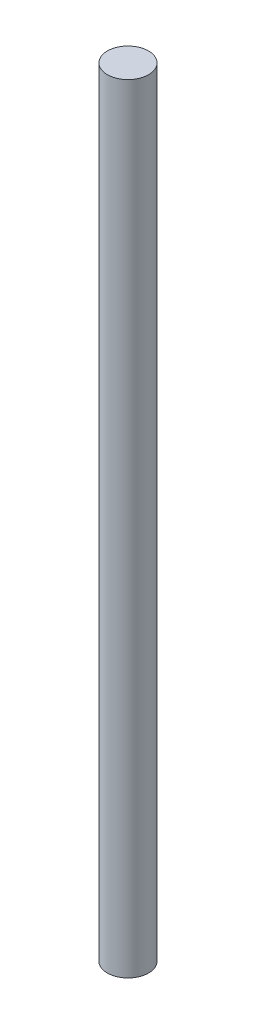
SolidWorks part; units mm, degrees
ref_plane "Front Plane" through (0, 0, 0) normal (0, 0, 1) x (1, 0, 0)
ref_plane "Top Plane" through (0, 0, 0) normal (0, 1, 0) x (1, 0, 0)
ref_plane "Right Plane" through (0, 0, 0) normal (1, 0, 0) x (0, 0, -1)
sketch "Sketch1" plane through (0, 0, 0) normal (0, 1, 0) x (1, 0, 0)
  circle A0 centre (0, 0) radius 6.35
  dimension "D1" = 12.7
extrude "Boss-Extrude1" add sketch "Sketch1" along normal mid plane 240
